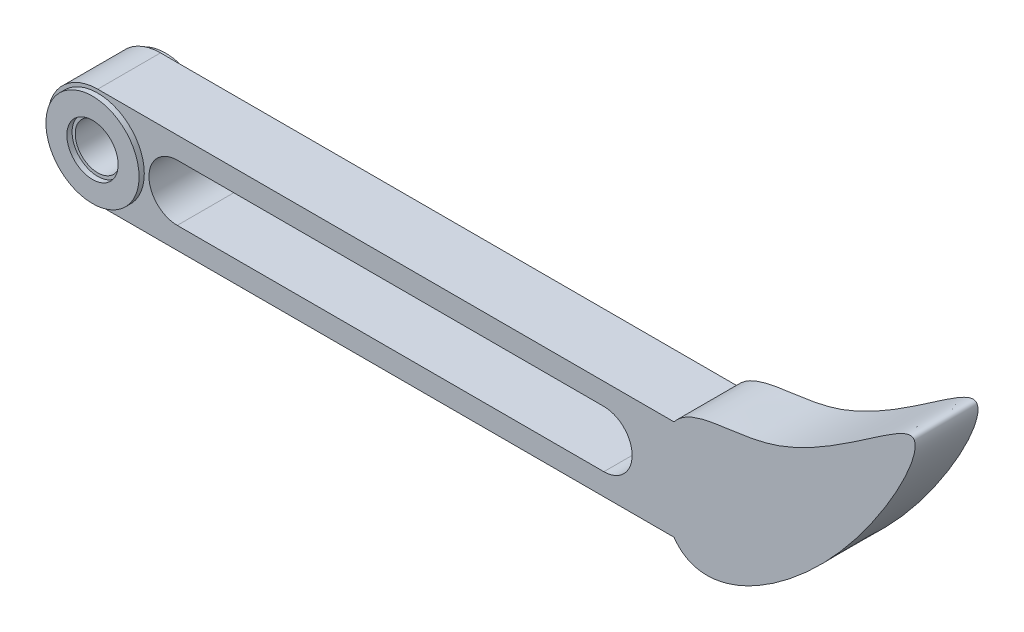
SolidWorks part; units mm, degrees
ref_plane "前视基准面" through (0, 0, 0) normal (0, 0, 1) x (1, 0, 0)
ref_plane "上视基准面" through (0, 0, 0) normal (0, 1, 0) x (1, 0, 0)
ref_plane "右视基准面" through (0, 0, 0) normal (1, 0, 0) x (0, 0, -1)
other "Configuration Table"
sketch "草图1" plane through (0, 0, 0) normal (0, 0, 1) x (1, 0, 0)
  line L0 (25.0569, 0) -> (-34.9431, 0) construction
  line L5 (25.0569, -4.773) -> (-34.9431, -4.773)
  line L6 (25.0569, 4.773) -> (-34.9431, 4.773)
  line L7 (25.0569, 4.773) -> (25.0569, -4.773)
  arc A1 (-34.9431, 4.773) -> (-34.9431, -4.773) centre (-34.9431, 0) ccw
  point P2 (0, 0)
  dimension "D1" = 60
extrude "凸台-拉伸1" add sketch "草图1" along normal mid plane 6
sketch "草图2" plane through (0, -0.227, -3) normal (0, 0, 1) x (1, 0, 0)
  line L0 (-22.4017, 0.227) -> (18.3569, 0.227) construction
  line L3 (0, -4.773) -> (0, 5.227) construction
  line L4 (25.0569, -4.5461) -> (25.0569, 5) construction
  line L8 (-22.4017, 2.927) -> (18.3569, 2.927)
  line L9 (-22.4017, -2.473) -> (18.3569, -2.473)
  arc A4 (-22.4017, 2.927) -> (-22.4017, -2.473) centre (-22.4017, 0.227) ccw
  arc A5 (18.3569, -2.473) -> (18.3569, 2.927) centre (18.3569, 0.227) ccw
  circle A6 centre (-30, 0.227) radius 2.15
  point P2 (-2.0224, 0.227)
  point P11 (21.0569, 0.227)
  dimension "D1" = 2.7
  dimension "D3" = 30
  dimension "D2" = 4.3
  dimension "D4" = 4
extrude "切除-拉伸2" cut sketch "草图2" against normal through all and the other way blind 10
sketch "草图6" plane through (0, 0, 3) normal (0, 0, 1) x (1, 0, 0)
  circle A0 centre (-30, 0) radius 2.45
extrude "拉伸-薄壁1" add sketch "草图6" along normal blind 0.5 thin
sketch "草图7" plane through (0, 0, -3) normal (0, 0, -1) x (-1, 0, 0)
  circle A0 centre (30, 0) radius 2.5
  dimension "D1" = 5
extrude "拉伸-薄壁2" add sketch "草图7" along normal blind 0.5 thin
sketch "草图9" plane through (0, 0, 3) normal (0, 0, 1) x (1, 0, 0)
  line L0 (25.0569, 4.773) -> (-34.9431, 4.773) construction
  line L1 (-34.9431, -4.773) -> (25.0569, -4.773) construction
  line L2 (-30, 4.773) -> (-45.2549, 4.773)
  line L3 (-45.2549, 4.773) -> (-45.2549, -4.773)
  line L4 (-45.2549, -4.773) -> (-30, -4.773)
  arc A0 (-30, 4.773) -> (-30, -4.773) centre (-30, 0) ccw
extrude "切除-拉伸3" cut sketch "草图9" against normal blind 10
sketch "草图11" plane through (0, 0, 3) normal (0, 0, 1) x (1, 0, 0)
  line L0 (25.0569, 4.773) -> (-30, 4.773) construction
  line L1 (25.0569, -4.773) -> (25.0569, 4.773) construction
  spline S0 degree 3 poles (23.1584, 7.5863) (23.7046, -11.0877) (41.5851, -0.8641) (52.8044, 21.6721) (36.4159, 5.4963) (23.1584, 7.5863) (23.7046, -11.0877) (41.5851, -0.8641) knots -0.519664 -0.287487 -0.143393 0 0.246516 0.480336 0.712513 0.856607 1 1.246516 1.480336 1.712513 only from (25.0569, -4.773) to (25.0569, -4.773)
extrude "凸台-拉伸2" add sketch "草图11" against normal up to surface (6 mm away) up to face at (-34.5, 0, -3)
